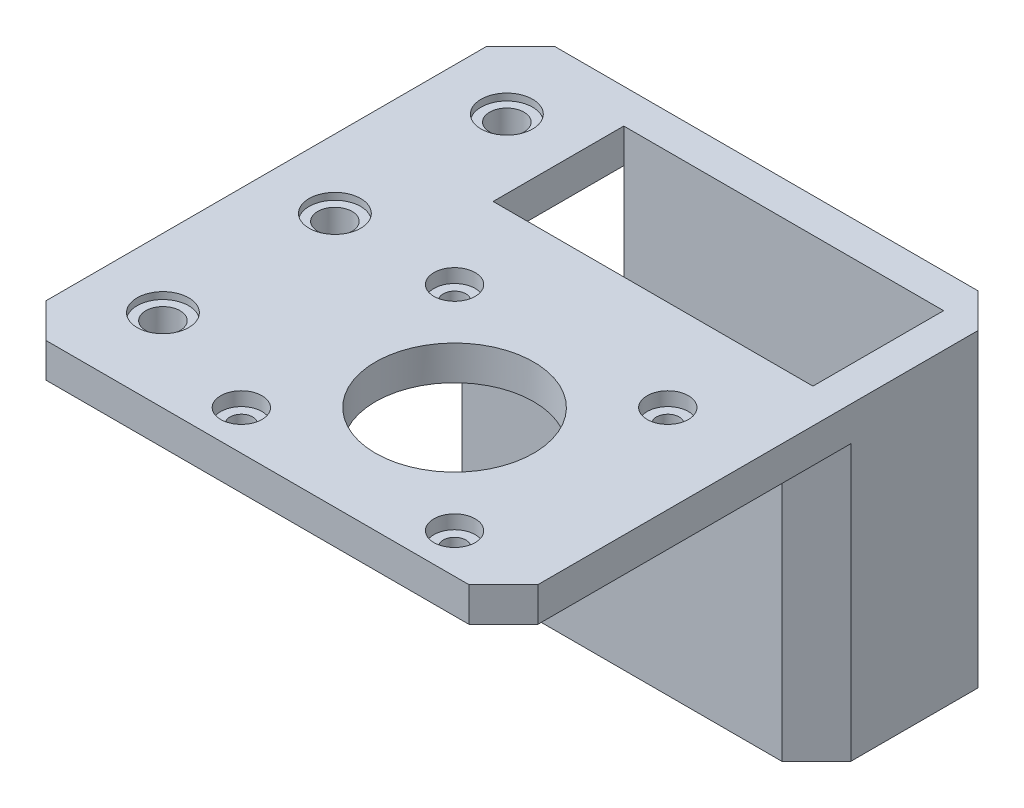
SolidWorks part; units mm, degrees
ref_plane "Front Plane" through (0, 0, 0) normal (0, 0, 1) x (1, 0, 0)
ref_plane "Top Plane" through (0, 0, 0) normal (0, 1, 0) x (1, 0, 0)
ref_plane "Right Plane" through (0, 0, 0) normal (1, 0, 0) x (0, 0, -1)
sketch "Sketch1" plane through (0, 0, 0) normal (0, 1, 0) x (1, 0, 0)
  line L0 (-23.25, 0) -> (23.25, 0) construction
  line L1 (-23.25, -9.5) -> (23.25, -9.5)
  line L2 (-23.25, -9.5) -> (-23.25, 9.5)
  line L3 (-23.25, 9.5) -> (23.25, 9.5)
  line L4 (23.25, -9.5) -> (23.25, 9.5)
  line L5 (-23.25, -9.5) -> (23.25, 9.5) construction
  line L6 (-23.25, 9.5) -> (23.25, -9.5) construction
  line L7 (0, 9.5) -> (0, -9.5) construction
  circle A0 centre (-18.5, 5) radius 2.15
  circle A1 centre (-18.5, -5) radius 2.15
  circle A2 centre (18.5, -5) radius 2.15
  circle A3 centre (18.5, 5) radius 2.15
  point P0 (0, 0)
  dimension "D3" = 4.3
  dimension "D4" = 18.5
  dimension "D5" = 5
  dimension "D1" = 19
  dimension "D2" = 46.5
extrude "Boss-Extrude1" add sketch "Sketch1" along normal blind 5
sketch "Sketch2" plane through (0, 0, 0) normal (0, 1, 0) x (1, 0, 0)
  line L0 (28.25, 14.5) -> (28.25, -14)
  line L1 (-23.25, -9.5) -> (23.25, -9.5)
  line L2 (-23.25, -9.5) -> (-23.25, -14)
  line L3 (-23.25, -14) -> (28.25, -14)
  line L5 (-23.25, 9.5) -> (23.25, 9.5)
  line L6 (-23.25, 9.5) -> (-23.25, 14.5)
  line L7 (-23.25, 14.5) -> (28.25, 14.5)
  line L12 (23.25, 9.5) -> (23.25, -9.5)
  dimension "D1" = 4.5
  dimension "D2" = 5
  dimension "D3" = 5
extrude "Boss-Extrude2" add sketch "Sketch2" along normal blind 45
sketch "Sketch6" plane through (0, 45, 0) normal (0, 1, 0) x (1, 0, 0)
  line L0 (-43.25, -9.5) -> (-43.25, -59.5) construction
  line L6 (28.25, -14) -> (-23.25, -14)
  line L7 (28.25, -14) -> (28.25, -59.5)
  line L8 (28.25, -59.5) -> (-43.25, -59.5)
  line L9 (-43.25, -9.5) -> (-43.25, -59.5)
  line L10 (-23.25, -9.5) -> (-43.25, -9.5)
  line L11 (-23.25, -9.5) -> (-23.25, -14)
  dimension "D1" = 45.5
  dimension "D2" = 20
extrude "Boss-Extrude5" add sketch "Sketch6" against normal blind 5
sketch "Sketch7" plane through (0, 45, 0) normal (0, 1, 0) x (1, 0, 0)
  line L0 (28.25, -59.5) -> (28.25, 14.5) construction
  line L1 (-43.25, -59.5) -> (28.25, -59.5) construction
  line L2 (-0.1, -38.25) -> (-0.1, -59.5) construction
  line L3 (-0.1, -38.25) -> (28.25, -38.25) construction
  circle A0 centre (-0.1, -38.25) radius 11.5
  circle A1 centre (-15.6, -22.75) radius 1.65
  circle A2 centre (15.4, -22.75) radius 1.65
  circle A3 centre (15.4, -53.75) radius 1.65
  circle A4 centre (-15.6, -53.75) radius 1.65
  dimension "D1" = 23
  dimension "D2" = 28.35
  dimension "D3" = 21.25
  dimension "D4" = 15.5
  dimension "D5" = 15.5
  dimension "D6" = 3.3
extrude "Cut-Extrude1" cut sketch "Sketch7" against normal up to next
sketch "Sketch8" plane through (-23.25, 0, 0) normal (-1, 0, 0) x (0, 0, 1)
  line L6 (-14.5, 45) -> (9.5, 45)
  line L7 (-14.5, 45) -> (-14.5, 40)
  line L8 (-14.5, 40) -> (9.5, 40)
  line L9 (9.5, 45) -> (9.5, 40)
extrude "Boss-Extrude6" add sketch "Sketch8" along normal blind 20
sketch "Sketch9" plane through (0, 45, 0) normal (0, 1, 0) x (1, 0, 0)
  line L0 (-33.25, 14.5) -> (-33.25, -59.5) construction
  line L1 (28.25, 14.5) -> (-43.25, 14.5) construction
  line L2 (-43.25, -59.5) -> (28.25, -59.5) construction
  line L3 (-43.25, 14.5) -> (-43.25, -59.5) construction
  circle A0 centre (-33.25, 2.5) radius 2.5
  circle A1 centre (-33.25, -22.5) radius 2.5
  circle A2 centre (-33.25, -47.5) radius 2.5
  dimension "D2" = 5
  dimension "D3" = 12
  dimension "D5" = 25
  dimension "D1" = 10
  dimension "D4" = 3
extrude "Cut-Extrude2" cut sketch "Sketch9" against normal up to next
chamfer "Chamfer1" distance 5 angle 45 5 edges at (28.25, 20, 14) (28.25, 22.5, -14.5) (28.25, 42.5, 59.5) (-43.25, 42.5, 59.5) (-43.25, 42.5, -14.5)
sketch "Sketch10" plane through (0, 45, 0) normal (0, 1, 0) x (1, 0, 0)
  circle A0 centre (-15.6, -22.75) radius 3
  circle A1 centre (15.4, -22.75) radius 3
  circle A2 centre (-15.6, -53.75) radius 3
  circle A3 centre (15.4, -53.75) radius 3
  dimension "D1" = 6
  dimension "D3" = 31
  dimension "D4" = 2
  dimension "D5" = 31
  dimension "D2" = 2
extrude "Cut-Extrude3" cut sketch "Sketch10" against normal blind 2
sketch "Sketch12" plane through (0, 0, 0) normal (0, -1, 0) x (1, 0, 0)
  line L0 (0, 0) -> (-23.25, 0) construction
  line L1 (-23.25, -9.5) -> (-23.25, 9.5) construction
  line L2 (0, 0) -> (0, 14) construction
  line L3 (-23.25, 14) -> (23.25, 14) construction
  circle A0 centre (-18.5, 5) radius 3.75
  circle A1 centre (-18.5, -5) radius 3.75
  circle A2 centre (18.5, -5) radius 3.75
  circle A3 centre (18.5, 5) radius 3.75
  dimension "D1" = 7.5
extrude "Cut-Extrude5" cut sketch "Sketch12" against normal blind 2
sketch "Sketch13" plane through (0, 45, 0) normal (0, 1, 0) x (1, 0, 0)
  circle A0 centre (-33.25, 2.5) radius 3.75
  circle A1 centre (-33.25, -22.5) radius 3.75
  circle A2 centre (-33.25, -47.5) radius 3.75
  dimension "D1" = 7.5
  dimension "D3" = 25
  dimension "D2" = 3
extrude "Cut-Extrude6" cut sketch "Sketch13" against normal blind 1
